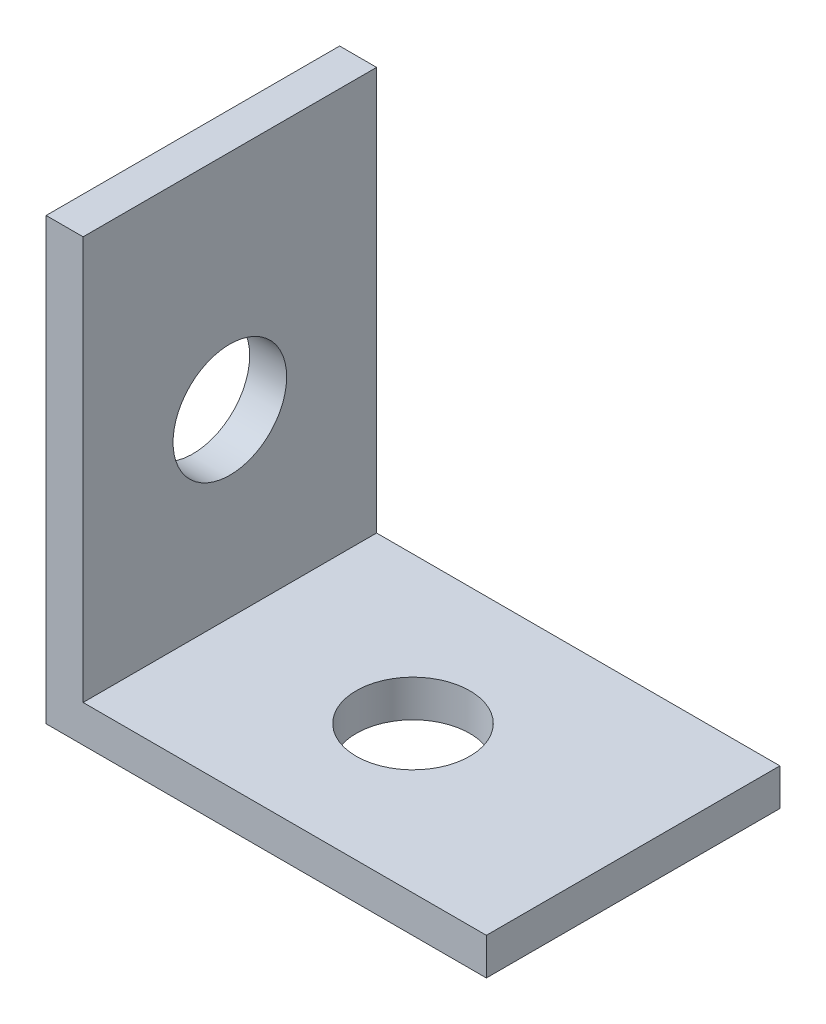
SolidWorks part; units mm, degrees
material "6061-T6 (SS)"
ref_plane "Front Plane" through (0, 0, 0) normal (0, 0, 1) x (1, 0, 0)
ref_plane "Top Plane" through (0, 0, 0) normal (0, 1, 0) x (1, 0, 0)
ref_plane "Right Plane" through (0, 0, 0) normal (1, 0, 0) x (0, 0, -1)
sketch "Sketch1" plane through (0, 0, 0) normal (0, 0, 1) x (1, 0, 0)
  line L0 (-3.4526, 16.0367) -> (-3.4526, -3.0133)
  line L1 (-3.4526, -3.0133) -> (15.5974, -3.0133)
  line L2 (15.5974, -3.0133) -> (15.5974, -1.4131)
  line L3 (15.5974, -1.4131) -> (-1.8524, -1.4131)
  line L4 (-1.8524, -1.4131) -> (-1.8524, 16.0367)
  line L5 (-1.8524, 16.0367) -> (-3.4526, 16.0367)
  dimension "D1" = 1.6002
  dimension "D2" = 19.05
extrude "Boss-Extrude1" add sketch "Sketch1" along normal blind 12.7
hole_wizard "#8 Clearance Hole1" positions "Sketch3" profile "Sketch2" hole size "#8" standard "ANSI Inch" end condition through all
sketch "Sketch3" plane through (0, -1.4131, 0) normal (0, 1, 0) x (1, 0, 0)
  line L0 (15.5974, -12.7) -> (15.5974, 0) construction
  line L3 (15.5974, 0) -> (-1.8524, 0) construction
  point P0 (6.0724, -6.35)
  dimension "D1" = 9.525
  dimension "D2" = 6.35
sketch "Sketch2" plane through (6.0724, -1.4131, 6.35) normal (1, 0, 0) x (0, 0, 1)
  line L0 (0, 0) -> (0, 1.6002)
  line L1 (0, 1.6002) -> (2.4574, 1.6002)
  line L2 (2.4574, 1.6002) -> (2.4574, 0)
  line L5 (2.4574, 0) -> (0, 0)
  line L11 (0, -6.35) -> (0, 107.95) construction
  dimension "Thru Hole Dia." = 4.9149
  dimension "Thru Hole Depth" = 1.6002
hole_wizard "#8 Clearance Hole2" positions "Sketch5" profile "Sketch4" hole size "#8" standard "ANSI Inch" end condition through all
sketch "Sketch5" plane through (-1.8524, 0, 0) normal (1, 0, 0) x (0, 0, -1)
  line L0 (-12.7, 16.0367) -> (0, 16.0367) construction
  line L2 (0, -1.4131) -> (0, 16.0367) construction
  point P0 (-6.35, 6.3847)
  dimension "D1" = 9.652
  dimension "D2" = 6.35
sketch "Sketch4" plane through (-1.8524, 6.3847, 6.35) normal (0, 1, 0) x (0, 0, -1)
  line L0 (0, 0) -> (0, 1.6002)
  line L1 (0, 1.6002) -> (2.4574, 1.6002)
  line L2 (2.4574, 1.6002) -> (2.4574, 0)
  line L5 (2.4574, 0) -> (0, 0)
  line L11 (0, -6.35) -> (0, 107.95) construction
  dimension "Thru Hole Dia." = 4.9149
  dimension "Thru Hole Depth" = 1.6002
